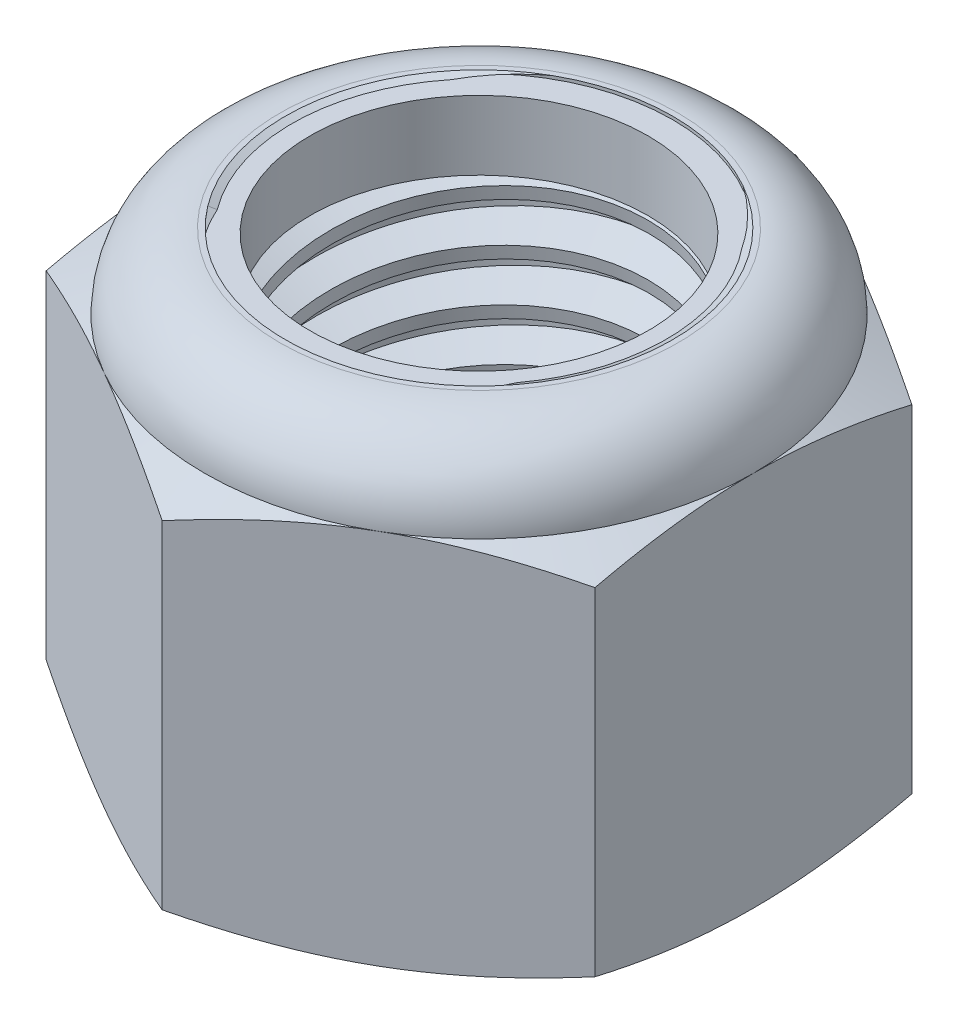
SolidWorks part; units mm, degrees
ref_plane "Front" through (0, 0, 0) normal (0, 0, 1) x (1, 0, 0)
ref_plane "Top" through (0, 0, 0) normal (0, 1, 0) x (1, 0, 0)
ref_plane "Right" through (0, 0, 0) normal (1, 0, 0) x (0, 0, -1)
sketch "Sketch1" plane through (0, 0, 0) normal (0, 1, 0) x (1, 0, 0)
  line L1 (0, 15.5812) -> (-13.4938, 7.7906)
  line L2 (-13.4938, 7.7906) -> (-13.4937, -7.7906)
  line L3 (-13.4937, -7.7906) -> (0, -15.5812)
  line L4 (0, -15.5812) -> (13.4937, -7.7906)
  line L5 (13.4937, -7.7906) -> (13.4937, 7.7906)
  line L6 (13.4937, 7.7906) -> (0, 15.5812)
  circle A0 centre (0, 0) radius 13.4938 construction
  dimension "Hex Flats" = 26.9875
extrude "Extrude1" add sketch "Sketch1" along normal blind 22.225
sketch "Sketch2" plane through (0, 0, 0) normal (1, 0, 0) x (0, 0, -1)
  line L0 (-9.525, 0) -> (-9.525, 22.225) construction
  line L1 (0, 0) -> (9.525, 0)
  line L2 (0, 0) -> (0, 22.225)
  line L3 (0, 22.225) -> (9.525, 22.225)
  line L4 (9.525, 0) -> (9.525, 22.225)
  line L5 (-7.7906, 22.225) -> (7.7906, 22.225) construction
  line L7 (0, -9.525) -> (0, 0) construction
  dimension "Thread Dia" = 19.05
revolve "Revolve1" add sketch "Sketch2" angle 360 about L7
sketch "Sketch3" plane through (0, 0, 0) normal (1, 0, 0) x (0, 0, -1)
  line L0 (9.525, 22.225) -> (-9.525, 22.225) construction
  line L1 (-9.525, 22.225) -> (-9.525, 19.685) construction
  line L2 (-9.525, 19.685) -> (9.525, 22.225) construction
  line L3 (9.525, 22.225) -> (9.567, 21.9103) construction
  line L4 (9.567, 21.9103) -> (9.8607, 19.7073)
  line L5 (9.8607, 19.7073) -> (8.393, 20.3124)
  line L6 (8.393, 20.3124) -> (8.3091, 20.9418)
  line L7 (8.3091, 20.9418) -> (9.567, 21.9103)
  line L8 (8.3511, 20.6271) -> (9.7138, 20.8088) construction
  line L9 (9.525, 22.225) -> (9.525, 20.7836) construction
  line L10 (9.525, 20.7836) -> (-9.525, 18.2436) construction
  line L11 (-9.525, 18.2436) -> (-9.525, 19.685) construction
  line L12 (-0.3615, 22.225) -> (0.3615, 16.8022) construction
  line L13 (-9.525, 0) -> (-9.525, 22.225) construction
  line L14 (0, 22.225) -> (9.525, 22.225) construction
  line L15 (9.525, 0) -> (9.525, 22.225) construction
  point P13 (0, 19.5136)
  dimension "D1" = 0.3175
  dimension "D2" = 0.635
  dimension "Thread Pitch" = 2.54
  dimension "D4" = 60
  dimension "D5" = 2.54
revolve "Cut-Revolve1" cut sketch "Sketch3" angle 360 about L12
pattern_linear "LPattern1" count 9 spacing 2.54 along (0, -1, 0) count 2 spacing 2.54 along (0, 1, 0) of "Cut-Revolve1"
sketch "Sketch4" plane through (0, 0, 0) normal (1, 0, 0) x (0, 0, -1)
  line L0 (0, 22.225) -> (9.525, 22.225)
  line L1 (9.525, 22.225) -> (8.3091, 21.658)
  line L2 (8.3091, 21.658) -> (8.3091, 0.567)
  line L3 (8.3091, 0.567) -> (9.525, 0)
  line L4 (9.525, 0) -> (0, 0)
  line L5 (0, 0) -> (0, 22.225)
  line L6 (9.525, 0) -> (9.525, 22.225) construction
  line L7 (0, 22.225) -> (9.525, 22.225) construction
  line L8 (0, 0) -> (9.525, 0) construction
  line L9 (0, 0) -> (0, 22.225) construction
  line L10 (0, 22.225) -> (0, 23.5666) construction
  dimension "D1" = 25
revolve "Cut-Revolve2" cut sketch "Sketch4" angle 360 about L10
combine bodies "Combine1" operation type subtract main body 112 bodies to subtract 111
sketch "Sketch5" plane through (0, 0, 0) normal (1, 0, 0) x (0, 0, -1)
  line L0 (0, 0) -> (13.4938, 0)
  line L1 (13.4938, 0) -> (15.5812, 0.9734)
  line L2 (15.5812, 0.9734) -> (15.5812, 17.5474)
  line L3 (15.5812, 17.5474) -> (13.4937, 18.5208)
  line L4 (9.7896, 22.225) -> (9.7896, 23.495)
  line L5 (9.7896, 23.495) -> (16.8512, 23.495)
  line L6 (16.8512, 23.495) -> (16.8512, -1.27)
  line L7 (16.8512, -1.27) -> (0, -1.27)
  line L8 (0, -1.27) -> (0, 0)
  line L9 (13.4937, 18.5208) -> (13.4938, 0) construction
  line L10 (0, 0) -> (9.525, 0) construction
  line L13 (15.5812, 9.2604) -> (16.8512, 9.2604) construction
  line L14 (15.5812, 22.225) -> (15.5812, 0) construction
  line L15 (0, 0) -> (0, 23.495) construction
  line L20 (0, 23.495) -> (9.7896, 23.495) construction
  line L22 (0, 22.225) -> (9.525, 22.225) construction
  arc A0 (13.4937, 18.5208) -> (9.7896, 22.225) centre (9.7896, 18.5208) ccw
  dimension "D1" = 25
  dimension "D2" = 1.27
  dimension "D3" = 22.225
  dimension "D4" = 3.7042
revolve "Cut-Revolve3" cut sketch "Sketch5" angle 360 about L15
sketch "Sketch6" plane through (0, 0, 0) normal (1, 0, 0) x (0, 0, -1)
  line L0 (0, 18.5208) -> (13.3413, 18.5208)
  line L1 (9.7896, 22.0726) -> (9.0493, 22.0726)
  line L2 (0, 23.495) -> (0, 18.5208)
  line L3 (9.0493, 23.495) -> (0, 23.495)
  line L4 (0, 23.495) -> (9.7896, 23.495) construction
  line L5 (0, 0) -> (0, 23.495) construction
  line L6 (0, 23.495) -> (0, 44.323) construction
  line L7 (9.0493, 22.0726) -> (9.0493, 23.495)
  line L8 (9.7896, 22.225) -> (9.7896, 22.0726) construction
  line L9 (9.0493, 22.0726) -> (8.3091, 22.0726) construction
  line L10 (8.3091, 22.0726) -> (8.3091, 21.658) construction
  arc A0 (13.3413, 18.5208) -> (9.7896, 22.0726) centre (9.7896, 18.5208) ccw
  arc A1 (13.4937, 18.5208) -> (9.7896, 22.225) centre (9.7896, 18.5208) ccw construction
  dimension "D1" = 0.1524
revolve "Cut-Revolve4" cut sketch "Sketch6" angle 360 about L6
sketch "Sketch7" plane through (0, 0, 0) normal (1, 0, 0) x (0, 0, -1)
  line L0 (8.3091, 18.597) -> (13.2643, 18.597)
  line L1 (9.7896, 21.9964) -> (8.3091, 21.9964)
  line L2 (8.3091, 21.9964) -> (8.3091, 18.597)
  line L3 (8.3091, 18.597) -> (0, 18.597) construction
  line L4 (0, 18.597) -> (0, 21.9964) construction
  line L5 (0, 21.9964) -> (8.3091, 21.9964) construction
  line L6 (8.3091, 18.597) -> (8.3091, 18.5208) construction
  line L7 (0, 18.5208) -> (13.3413, 18.5208) construction
  line L8 (9.7896, 21.9964) -> (9.7896, 22.0726) construction
  arc A0 (13.2643, 18.597) -> (9.7896, 21.9964) centre (9.7896, 18.5208) ccw
  arc A2 (13.3413, 18.5208) -> (9.7896, 22.0726) centre (9.7896, 18.5208) ccw construction
  dimension "D1" = 0.0762
revolve "Revolve2" add sketch "Sketch7" angle 360 about L4
equation "\"D1@Sketch3\"=\"Thread Pitch@Sketch3\"/8"
equation "\"D2@Sketch3\"=\"Thread Pitch@Sketch3\"/4"
equation "\"D5@Sketch3\"=\"Thread Pitch@Sketch3\""
equation "\"D4@LPattern1\"=\"Thread Pitch@Sketch3\""
equation "\"D3@LPattern1\"=\"Thread Pitch@Sketch3\""
equation "\"D1@LPattern1\"=\"Height@Extrude1\"/\"Thread Pitch@Sketch3\""
equation "\"D4@Sketch5\"=\"Height@Extrude1\"/6"
